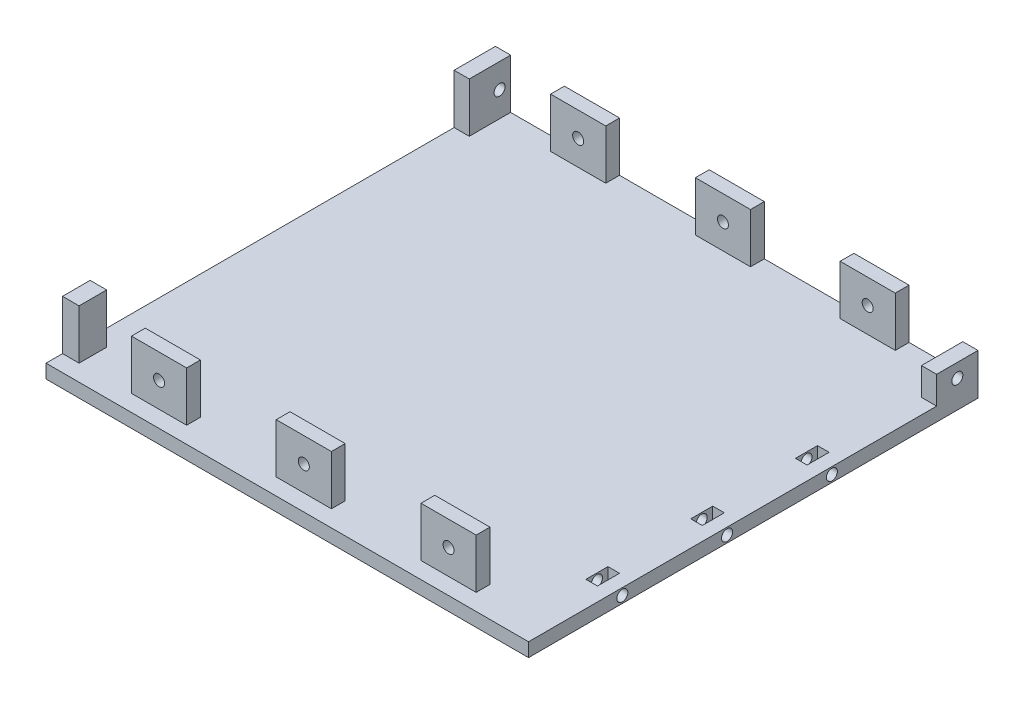
SolidWorks part; units mm, degrees
ref_plane "Front Plane" through (0, 0, 0) normal (0, 0, 1) x (1, 0, 0)
ref_plane "Top Plane" through (0, 0, 0) normal (0, 1, 0) x (1, 0, 0)
ref_plane "Right Plane" through (0, 0, 0) normal (1, 0, 0) x (0, 0, -1)
sketch "Sketch1" plane through (0, 0, 0) normal (0, 1, 0) x (1, 0, 0)
  line L1 (-151.5464, 68.5567) -> (23.4536, 68.5567)
  line L2 (-151.5464, 68.5567) -> (-151.5464, -94.4433)
  line L3 (-151.5464, -94.4433) -> (23.4536, -94.4433)
  line L4 (23.4536, 68.5567) -> (23.4536, -94.4433)
  dimension "D1" = 163
  dimension "D2" = 175
extrude "Boss-Extrude1" add sketch "Sketch1" along normal blind 5
sketch "Sketch2" plane through (0, 5, 0) normal (0, 1, 0) x (1, 0, 0)
  line L0 (23.4536, 68.5567) -> (-151.5464, 68.5567) construction
  line L1 (-126.5464, 68.5567) -> (-106.5464, 68.5567)
  line L2 (-126.5464, 68.5567) -> (-126.5464, 63.5567)
  line L3 (-126.5464, 63.5567) -> (-106.5464, 63.5567)
  line L4 (-106.5464, 68.5567) -> (-106.5464, 63.5567)
  line L5 (-151.5464, 68.5567) -> (-151.5464, -94.4433) construction
  line L7 (-126.5464, -88.4433) -> (-106.5464, -88.4433)
  line L8 (-126.5464, -88.4433) -> (-126.5464, -83.4433)
  line L9 (-126.5464, -83.4433) -> (-106.5464, -83.4433)
  line L10 (-106.5464, -88.4433) -> (-106.5464, -83.4433)
  line L11 (23.4536, -94.4433) -> (23.4536, 68.5567) construction
  line L12 (-1.5464, -83.4433) -> (-21.5464, -83.4433)
  line L13 (-1.5464, -83.4433) -> (-1.5464, -88.4433)
  line L14 (-1.5464, -88.4433) -> (-21.5464, -88.4433)
  line L15 (-21.5464, -83.4433) -> (-21.5464, -88.4433)
  line L17 (-1.5464, 63.5567) -> (-21.5464, 63.5567)
  line L18 (-1.5464, 63.5567) -> (-1.5464, 68.5567)
  line L19 (-1.5464, 68.5567) -> (-21.5464, 68.5567)
  line L20 (-21.5464, 63.5567) -> (-21.5464, 68.5567)
  line L22 (-74.0464, -83.4433) -> (-54.0464, -83.4433)
  line L23 (-74.0464, -83.4433) -> (-74.0464, -88.4433)
  line L24 (-74.0464, -88.4433) -> (-54.0464, -88.4433)
  line L25 (-54.0464, -83.4433) -> (-54.0464, -88.4433)
  line L26 (-74.0464, 63.5567) -> (-54.0464, 63.5567)
  line L27 (-74.0464, 63.5567) -> (-74.0464, 68.5567)
  line L28 (-74.0464, 68.5567) -> (-54.0464, 68.5567)
  line L29 (-54.0464, 63.5567) -> (-54.0464, 68.5567)
  point P28 (-106.5464, 66.0567)
  dimension "D1" = 25
  dimension "D2" = 5
  dimension "D3" = 20
  dimension "D4" = 20
  dimension "D5" = 5
  dimension "D6" = 25
  dimension "D7" = 20
  dimension "D8" = 5
  dimension "D9" = 25
  dimension "D10" = 20
  dimension "D11" = 5
  dimension "D12" = 25
  dimension "D13" = 157
  dimension "D14" = 157
  dimension "D15" = 5
  dimension "D16" = 20
  dimension "D17" = 32.5
  dimension "D18" = 32.5
  dimension "D19" = 32.5
  dimension "D20" = 20
  dimension "D21" = 32.5
extrude "Boss-Extrude2" add sketch "Sketch2" along normal blind 18
sketch "Sketch3" plane through (0, 0, 88.4433) normal (0, 0, 1) x (1, 0, 0)
  line L0 (-126.5464, 5) -> (-106.5464, 5) construction
  line L1 (-126.5464, 23) -> (-126.5464, 5) construction
  line L2 (-74.0464, 23) -> (-74.0464, 5) construction
  line L3 (-21.5464, 23) -> (-21.5464, 5) construction
  circle A0 centre (-116.5464, 14.1) radius 2
  circle A1 centre (-64.0464, 14.1) radius 2
  circle A2 centre (-11.5464, 14.1) radius 2
  dimension "D1" = 9.1
  dimension "D3" = 10
  dimension "D4" = 10
  dimension "D2" = 10
extrude "Cut-Extrude1" cut sketch "Sketch3" against normal through all both and the other way through all
sketch "Sketch4" plane through (0, 5, 0) normal (0, 1, 0) x (1, 0, 0)
  line L0 (-151.5464, 68.5567) -> (-151.5464, -94.4433) construction
  line L1 (-151.5464, 68.5567) -> (-146.0464, 68.5567)
  line L2 (-151.5464, 68.5567) -> (-151.5464, 53.5567)
  line L3 (-151.5464, 53.5567) -> (-146.0464, 53.5567)
  line L4 (-146.0464, 68.5567) -> (-146.0464, 53.5567)
  line L5 (-151.5464, -88.4433) -> (-145.5464, -88.4433)
  line L6 (-151.5464, -88.4433) -> (-151.5464, -78.4433)
  line L7 (-151.5464, -78.4433) -> (-145.5464, -78.4433)
  line L8 (-145.5464, -88.4433) -> (-145.5464, -78.4433)
  line L9 (-151.5464, -94.4433) -> (23.4536, -94.4433) construction
  dimension "D1" = 15
  dimension "D2" = 5.5
  dimension "D3" = 6
  dimension "D4" = 6
  dimension "D5" = 10
extrude "Boss-Extrude3" add sketch "Sketch4" along normal blind 18
sketch "Sketch5" plane through (-146.0464, 0, 0) normal (1, 0, 0) x (0, 0, -1)
  line L0 (68.5567, 23) -> (68.5567, 0) construction
  line L1 (53.5567, 5) -> (68.5567, 5) construction
  circle A0 centre (64.5567, 14.1) radius 2
  dimension "D1" = 4
  dimension "D2" = 9.1
extrude "Cut-Extrude2" cut sketch "Sketch5" against normal blind 18
sketch "Sketch6" plane through (0, 5, 0) normal (0, 1, 0) x (1, 0, 0)
  line L1 (23.4536, 68.5567) -> (17.9536, 68.5567)
  line L2 (23.4536, 68.5567) -> (23.4536, 53.5567)
  line L3 (23.4536, 53.5567) -> (17.9536, 53.5567)
  line L4 (17.9536, 68.5567) -> (17.9536, 53.5567)
  dimension "D1" = 5.5
  dimension "D2" = 15
extrude "Boss-Extrude4" add sketch "Sketch6" along normal blind 10
sketch "Sketch7" plane through (23.4536, 0, 0) normal (1, 0, 0) x (0, 0, -1)
  line L0 (68.5567, 15) -> (68.5567, 0) construction
  line L2 (53.5567, 15) -> (68.5567, 15) construction
  circle A1 centre (61.0567, 10) radius 2
  dimension "D1" = 7.5
  dimension "D2" = 5
extrude "Cut-Extrude3" cut sketch "Sketch7" against normal blind 10 contours A1
sketch "Sketch8" plane through (0, 5, 0) normal (0, 1, 0) x (1, 0, 0)
  line L1 (14.2536, -56.4433) -> (18.4536, -56.4433)
  line L2 (14.2536, -56.4433) -> (14.2536, -64.4433)
  line L3 (14.2536, -64.4433) -> (18.4536, -64.4433)
  line L4 (18.4536, -56.4433) -> (18.4536, -64.4433)
  line L5 (23.4536, -94.4433) -> (23.4536, 53.5567) construction
  line L6 (-151.5464, -94.4433) -> (23.4536, -94.4433) construction
  line L8 (14.2536, -26.4433) -> (18.4536, -26.4433)
  line L9 (14.2536, -26.4433) -> (14.2536, -18.4433)
  line L10 (14.2536, -18.4433) -> (18.4536, -18.4433)
  line L11 (18.4536, -26.4433) -> (18.4536, -18.4433)
  line L12 (14.2536, 11.5567) -> (18.4536, 11.5567)
  line L13 (14.2536, 11.5567) -> (14.2536, 19.5567)
  line L14 (14.2536, 19.5567) -> (18.4536, 19.5567)
  line L15 (18.4536, 11.5567) -> (18.4536, 19.5567)
  dimension "D1" = 30
  dimension "D2" = 4.2
  dimension "D3" = 8
  dimension "D4" = 5
  dimension "D5" = 4.2
  dimension "D6" = 8
  dimension "D7" = 30
  dimension "D8" = 8
  dimension "D9" = 30
extrude "Cut-Extrude4" cut sketch "Sketch8" against normal blind 10
sketch "Sketch9" plane through (23.4536, 0, 0) normal (1, 0, 0) x (0, 0, -1)
  line L0 (-94.4433, 5) -> (53.5567, 5) construction
  line L1 (-94.4433, 5) -> (-94.4433, 0) construction
  circle A0 centre (-60.4433, 2.5) radius 2
  circle A2 centre (15.5567, 2.5) radius 2
  circle A3 centre (-22.4433, 2.5) radius 2
  dimension "D1" = 2.5
  dimension "D2" = 2.5
  dimension "D3" = 2.5
  dimension "D4" = 34
  dimension "D5" = 38
  dimension "D6" = 38
extrude "Cut-Extrude5" cut sketch "Sketch9" against normal blind 18
